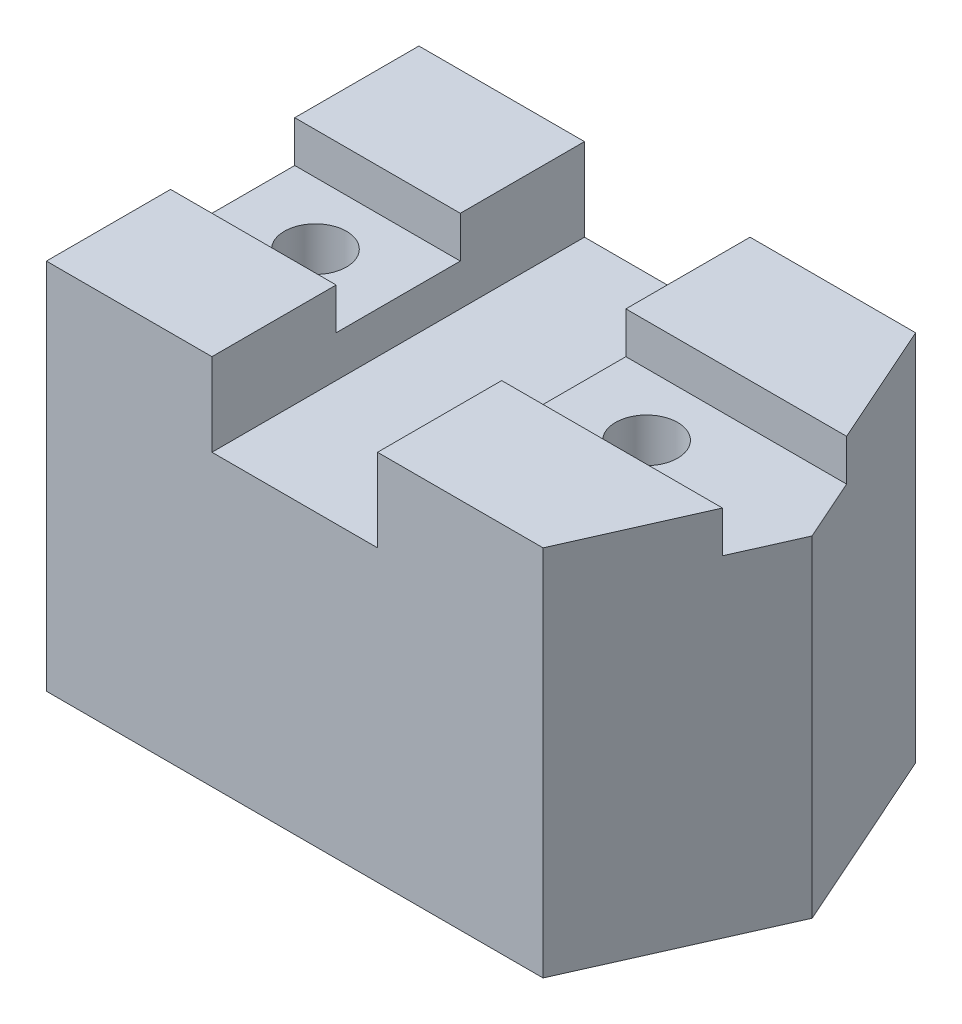
SolidWorks part; units mm, degrees
ref_plane "Front Plane" through (0, 0, 0) normal (0, 0, 1) x (1, 0, 0)
ref_plane "Top Plane" through (0, 0, 0) normal (0, 1, 0) x (1, 0, 0)
ref_plane "Right Plane" through (0, 0, 0) normal (1, 0, 0) x (0, 0, -1)
sketch "Sketch2" plane through (0, 0, 0) normal (0, 1, 0) x (1, 0, 0)
  line L0 (0, 0) -> (152.4, 0)
  line L1 (152.4, 0) -> (177.8, 57.15)
  line L2 (177.8, 57.15) -> (152.4, 114.3)
  line L3 (152.4, 114.3) -> (0, 114.3)
  line L4 (0, 114.3) -> (0, 0)
  dimension "D1" = 114.3
  dimension "D2" = 177.8
  dimension "D3" = 152.4
extrude "Boss-Extrude1" add sketch "Sketch2" along normal blind 114.3
sketch "Sketch3" plane through (0, 114.3, 0) normal (0, 1, 0) x (1, 0, 0)
  line L0 (169.3333, 38.1) -> (0, 38.1)
  line L1 (152.4, 0) -> (177.8, 57.15) construction
  line L2 (0, 114.3) -> (0, 0) construction
  line L7 (0, 38.1) -> (0, 76.2)
  line L8 (0, 76.2) -> (267.804, 76.2)
  line L9 (267.804, 76.2) -> (218.0117, 38.1)
  line L10 (218.0117, 38.1) -> (169.3333, 38.1)
  dimension "D1" = 38.1
  dimension "D2" = 38.1
  dimension "D3" = 267.804
  dimension "D4" = 48.6784
extrude "Cut-Extrude4" cut sketch "Sketch3" against normal blind 12.7
sketch "Sketch5" plane through (0, 114.3, 0) normal (0, 1, 0) x (1, 0, 0)
  line L0 (50.8, 0) -> (50.8, 114.3)
  line L1 (0, 0) -> (152.4, 0) construction
  line L2 (152.4, 114.3) -> (0, 114.3) construction
  line L3 (50.8, 114.3) -> (101.6, 114.3)
  line L4 (101.6, 114.3) -> (101.6, 0)
  line L5 (101.6, 0) -> (50.8, 0)
  dimension "D1" = 50.8
  dimension "D2" = 50.8
extrude "Cut-Extrude5" cut sketch "Sketch5" against normal blind 25.4
sketch "Sketch6" plane through (0, 101.6, 0) normal (0, 1, 0) x (1, 0, 0)
  line L0 (101.6, 38.1) -> (169.3333, 38.1) construction
  circle A0 centre (127, 57.15) radius 9.525
  dimension "D1" = 19.05
  dimension "D2" = 50.8
  dimension "D3" = 19.05
extrude "Cut-Extrude6" cut sketch "Sketch6" against normal blind 2286
sketch "Sketch7" plane through (0, 101.6, 0) normal (0, 1, 0) x (1, 0, 0)
  line L0 (50.8, 76.2) -> (0, 76.2) construction
  line L1 (0, 76.2) -> (0, 38.1) construction
  circle A0 centre (25.4, 57.15) radius 9.525
  dimension "D1" = 19.05
  dimension "D2" = 19.05
  dimension "D3" = 25.4
extrude "Cut-Extrude7" cut sketch "Sketch7" against normal blind 2286
